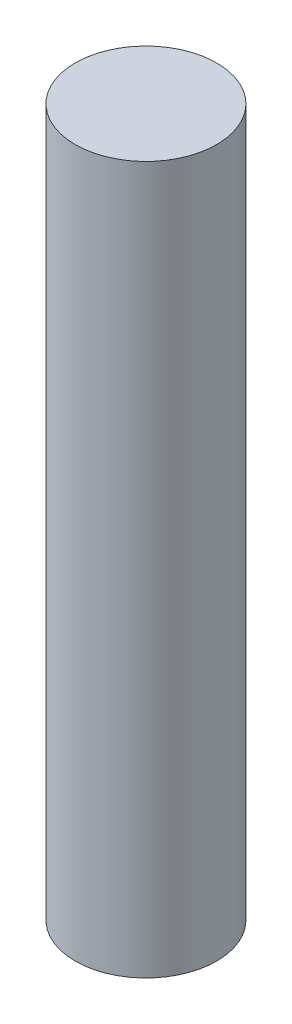
SolidWorks part; units mm, degrees
ref_plane "Front Plane" through (0, 0, 0) normal (0, 0, 1) x (1, 0, 0)
ref_plane "Top Plane" through (0, 0, 0) normal (0, 1, 0) x (1, 0, 0)
ref_plane "Right Plane" through (0, 0, 0) normal (1, 0, 0) x (0, 0, -1)
sketch "Sketch2" plane through (0, 0, 0) normal (0, 1, 0) x (1, 0, 0)
  circle A0 centre (0, 0) radius 2
  dimension "D1" = 4
extrude "Boss-Extrude1" add sketch "Sketch2" along normal blind 20
